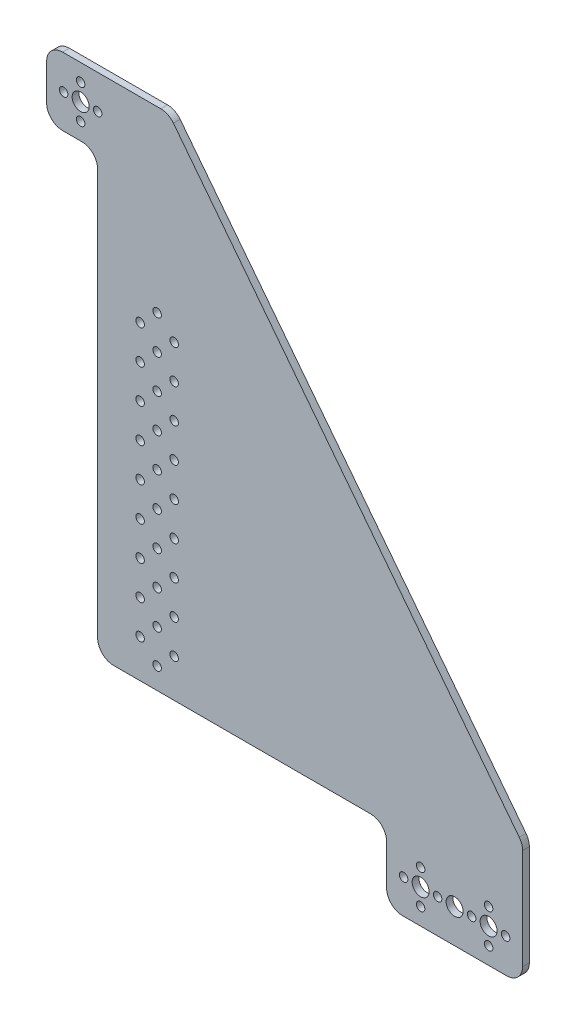
SolidWorks part; units mm, degrees
ref_plane "Front" through (0, 0, 0) normal (0, 0, 1) x (1, 0, 0)
ref_plane "Top" through (0, 0, 0) normal (0, 1, 0) x (1, 0, 0)
ref_plane "Right" through (0, 0, 0) normal (1, 0, 0) x (0, 0, -1)
sketch "Sketch1" plane through (0, 0, 0) normal (0, 0, 1) x (1, 0, 0)
  line L0 (176, -244) -> (176, -236) construction
  line L1 (144, -229.5) -> (144, -248.5)
  line L2 (151.5, -256) -> (200.5, -256)
  line L3 (208, -248.5) -> (208, -201.1695)
  line L4 (206.4243, -196.5703) -> (43.652, 13.0992)
  line L5 (37.7277, 16) -> (-8.5, 16)
  line L6 (-16, 8.5) -> (-16, -8.5)
  line L7 (-8.5, -16) -> (0.5, -16)
  line L8 (8, -23.5) -> (8, -214.5)
  line L9 (15.5, -222) -> (136.5, -222)
  line L10 (44, -204) -> (44, -188) construction
  circle A0 centre (0, 0) radius 4
  circle A1 centre (0, 8) radius 2
  circle A4 centre (160, -240) radius 4
  circle A5 centre (176, -240) radius 4
  circle A6 centre (160, -232) radius 2
  circle A7 centre (168, -240) radius 2
  circle A8 centre (160, -248) radius 2
  circle A9 centre (152, -240) radius 2
  circle A10 centre (200, -240) radius 2
  circle A11 centre (192, -248) radius 2
  circle A12 centre (192, -240) radius 4
  circle A13 centre (184, -240) radius 2
  circle A14 centre (192, -232) radius 2
  circle A15 centre (8, 0) radius 2
  circle A16 centre (0, -8) radius 2
  circle A17 centre (-8, 0) radius 2
  arc A18 (0.5, -16) -> (8, -23.5) centre (0.5, -23.5) cw
  arc A19 (-16, -8.5) -> (-8.5, -16) centre (-8.5, -8.5) ccw
  arc A20 (-8.5, 16) -> (-16, 8.5) centre (-8.5, 8.5) ccw
  arc A21 (43.652, 13.0992) -> (37.7277, 16) centre (37.7277, 8.5) ccw
  arc A22 (208, -201.1695) -> (206.4243, -196.5703) centre (200.5, -201.1695) ccw
  arc A23 (200.5, -256) -> (208, -248.5) centre (200.5, -248.5) ccw
  arc A24 (144, -248.5) -> (151.5, -256) centre (151.5, -248.5) ccw
  arc A25 (144, -229.5) -> (136.5, -222) centre (136.5, -229.5) ccw
  arc A26 (8, -214.5) -> (15.5, -222) centre (15.5, -214.5) ccw
  circle A27 centre (36, -212) radius 2
  circle A28 centre (28, -204) radius 2
  circle A29 centre (36, -196) radius 2
  circle A30 centre (44, -204) radius 2
  circle A31 centre (44, -188) radius 2
  circle A32 centre (36, -180) radius 2
  circle A33 centre (28, -188) radius 2
  circle A34 centre (44, -172) radius 2
  circle A35 centre (36, -164) radius 2
  circle A36 centre (28, -172) radius 2
  circle A37 centre (44, -156) radius 2
  circle A38 centre (36, -148) radius 2
  circle A39 centre (28, -156) radius 2
  circle A40 centre (44, -140) radius 2
  circle A41 centre (36, -132) radius 2
  circle A42 centre (28, -140) radius 2
  circle A43 centre (44, -124) radius 2
  circle A44 centre (36, -116) radius 2
  circle A45 centre (28, -124) radius 2
  circle A46 centre (44, -108) radius 2
  circle A47 centre (36, -100) radius 2
  circle A48 centre (28, -108) radius 2
  circle A49 centre (44, -92) radius 2
  circle A50 centre (36, -84) radius 2
  circle A51 centre (28, -92) radius 2
  circle A52 centre (44, -76) radius 2
  circle A53 centre (36, -68) radius 2
  circle A54 centre (28, -76) radius 2
  point P20 (160, -240)
  point P25 (176, -240)
  point P40 (0, 0)
  point P54 (8, -16)
  point P59 (-16, 16)
  point P62 (41.4, 16)
  point P65 (208, -198.6)
  point P68 (208, -256)
  point P81 (36, -204)
  dimension "D1" = 4
  dimension "D2" = 8
  dimension "D19" = 7.5
  dimension "D3" = 8
  dimension "D4" = 8
  dimension "D5" = 240
  dimension "D6" = 160
  dimension "D7" = 16
  dimension "D10" = 16
  dimension "D11" = 16
  dimension "D12" = 16
  dimension "D13" = 16
  dimension "D14" = 16
  dimension "D15" = 16
  dimension "D16" = 57.4
  dimension "D17" = 57.4
  dimension "D18" = 18
  dimension "D21" = 8
  dimension "D22" = 10
  dimension "D23" = 20
  dimension "D25" = 16
  dimension "D24" = 9
  dimension "D8" = 4
  dimension "D9" = 4
  dimension "D20" = 4
extrude "Boss-Extrude1" add sketch "Sketch1" along normal blind 3.175
sketch "Sketch2" plane through (0, 0, 3.175) normal (0, 0, 1) x (1, 0, 0)
  line L3 (146.2334, -243.2982) -> (-16.5389, -33.6287)
  line L4 (146.2334, -243.2982) -> (-16.5389, -33.6287) construction
  text T0 "8699" font "Century Gothic" height 63.5
  dimension "D1" = 76.2
